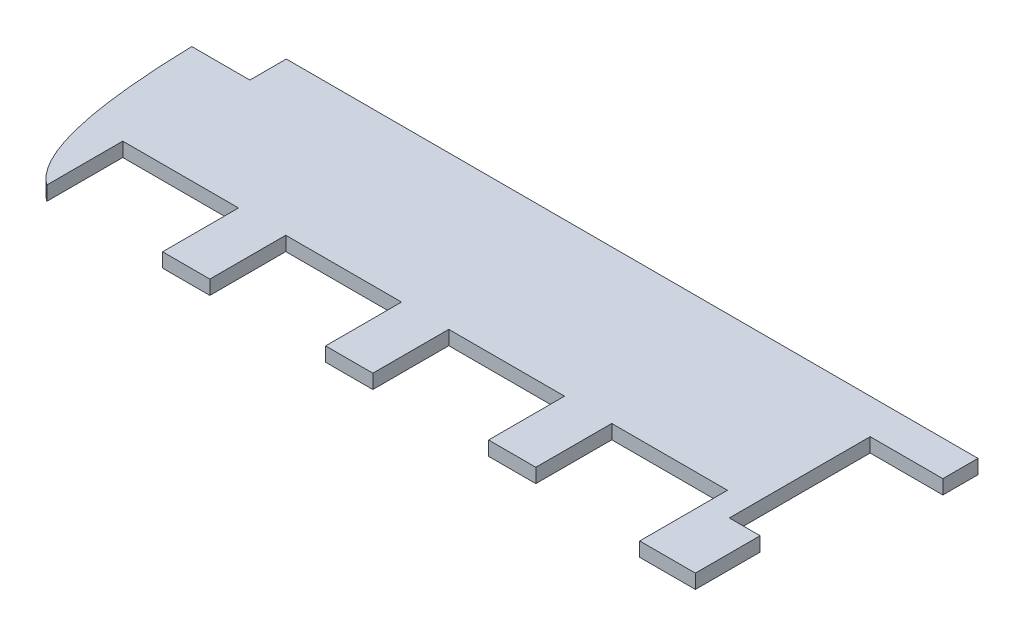
SolidWorks part; units mm, degrees
ref_plane "Front Plane" through (0, 0, 0) normal (0, 0, 1) x (1, 0, 0)
ref_plane "Top Plane" through (0, 0, 0) normal (0, 1, 0) x (1, 0, 0)
ref_plane "Right Plane" through (0, 0, 0) normal (1, 0, 0) x (0, 0, -1)
sketch "Sketch1" plane through (0, 0, 0) normal (0, 1, 0) x (1, 0, 0)
  line L0 (-23.2479, 15.8012) -> (54.7521, 15.8012)
  line L1 (-23.2479, 15.8012) -> (-23.2479, 11.6912)
  line L2 (-23.2479, 11.6912) -> (-29.7979, 11.6912)
  line L3 (54.7521, 15.8012) -> (54.7521, 11.8412)
  line L4 (54.7521, 11.8412) -> (46.5521, 11.8412)
  line L5 (46.5521, 11.8412) -> (46.5521, -4.0388)
  line L6 (46.5521, -4.0388) -> (50.0221, -4.0388)
  line L7 (50.0221, -4.0388) -> (50.0221, -11.3388)
  line L8 (50.0221, -11.3388) -> (43.7421, -11.3388)
  line L9 (43.7421, -11.3388) -> (43.7421, -1.4388)
  line L10 (43.7421, -1.4388) -> (30.6921, -1.4388)
  line L11 (30.6921, -1.4388) -> (30.6921, -9.9988)
  line L12 (30.6921, -9.9988) -> (25.3621, -9.9988)
  line L13 (12.3121, -9.9988) -> (6.9821, -9.9988)
  line L14 (12.3121, -1.4388) -> (12.3121, -9.9988)
  line L15 (25.3621, -1.4388) -> (12.3121, -1.4388)
  line L16 (25.3621, -9.9988) -> (25.3621, -1.4388)
  line L17 (-6.0679, -9.9988) -> (-11.3979, -9.9988)
  line L18 (-6.0679, -1.4388) -> (-6.0679, -9.9988)
  line L19 (6.9821, -1.4388) -> (-6.0679, -1.4388)
  line L20 (6.9821, -9.9988) -> (6.9821, -1.4388)
  line L22 (-24.4479, -1.4388) -> (-24.4479, -9.9988)
  line L23 (-11.3979, -1.4388) -> (-24.4479, -1.4388)
  line L24 (-11.3979, -9.9988) -> (-11.3979, -1.4388)
  line L25 (30.6921, -9.9988) -> (12.3121, -9.9988) construction
  line L26 (-24.4479, -9.9988) -> (-29.7779, -9.9988) [skipped]
  spline S0 degree 2 poles (-24.4479, -9.9988) (-29.3411, -6.5186) (-29.7979, 11.6912) knots 0 0 0 1 1 1
  dimension "D1" = 78
  dimension "D2" = 4.11
  dimension "D3" = 6.55
  dimension "D4" = 3.96
  dimension "D5" = 8.2
  dimension "D6" = 15.88
  dimension "D7" = 3.47
  dimension "D8" = 7.3
  dimension "D9" = 6.28
  dimension "D10" = 9.9
  dimension "D11" = 13.05
  dimension "D12" = 8.56
  dimension "D13" = 5.33
  dimension "D14" = 4
extrude "Boss-Extrude1" add sketch "Sketch1" along normal blind 1.6
